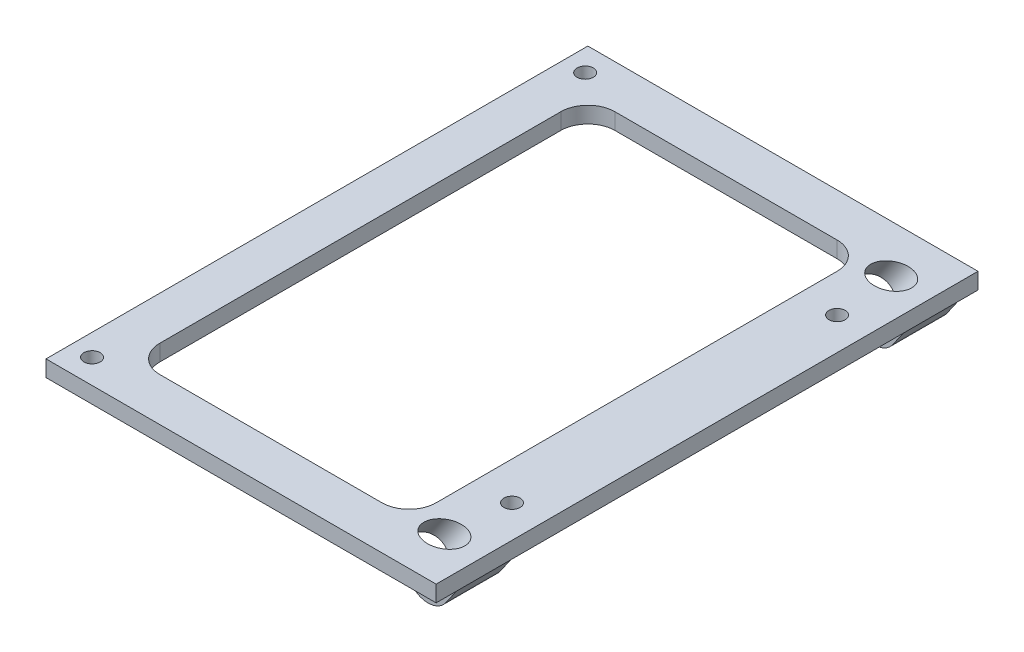
SolidWorks part; units mm, degrees
material "PET"
ref_plane "Front Plane" through (0, 0, 0) normal (0, 0, 1) x (1, 0, 0)
ref_plane "Top Plane" through (0, 0, 0) normal (0, 1, 0) x (1, 0, 0)
ref_plane "Right Plane" through (0, 0, 0) normal (1, 0, 0) x (0, 0, -1)
sketch "Sketch1" plane through (0, 0, 0) normal (0, -1, 0) x (1, 0, 0)
  line L15 (508.5, -88) -> (508.5, 88)
  line L16 (508.5, 88) -> (0.8696, 88)
  line L17 (0.8696, 88) -> (0.8696, -88)
  line L18 (0.8696, -88) -> (508.5, -88)
  line L19 (508.5, -88) -> (508.5, 88)
  line L20 (508.5, 88) -> (0.8696, 88)
  line L21 (0.8696, 88) -> (0.8696, -88)
  line L22 (0.8696, -88) -> (508.5, -88)
  line L54 (11, 0) -> (62, 0) construction
  line L55 (36.5, -42) -> (36.5, 42) construction
  line L57 (70, -50) -> (3, -50)
  line L58 (62, -37) -> (62, 37)
  line L59 (16, -42) -> (57, -42)
  line L60 (57, 42) -> (16, 42)
  line L61 (11, 37) -> (11, -37)
  line L62 (62, -37) -> (62, 37)
  line L63 (16, -42) -> (57, -42)
  line L64 (57, 42) -> (16, 42)
  line L65 (11, 37) -> (11, -37)
  line L66 (70, -50) -> (70, 50)
  line L67 (70, 50) -> (3, 50)
  line L68 (3, -50) -> (3, 50)
  line L69 (70, -50) -> (3, 50) construction
  line L70 (70, 50) -> (3, -50) construction
  line L2167 (70, 50) -> (75, 50)
  line L2168 (70, 50) -> (70, -50)
  line L2169 (70, -50) -> (75, -50)
  line L2170 (75, 50) -> (75, -50)
  circle A3 centre (7, -45.5) radius 1.5
  circle A4 centre (7, -45.5) radius 1.5
  circle A6 centre (7, 45.5) radius 1.5
  circle A7 centre (7, 45.5) radius 1.5
  circle A9 centre (66, -45.5) radius 1.5
  circle A10 centre (66, -45.5) radius 1.5
  circle A12 centre (66, 45.5) radius 1.5
  circle A13 centre (66, 45.5) radius 1.5
  arc A46 (62, 37) -> (57, 42) centre (57, 37) ccw
  arc A47 (57, -42) -> (62, -37) centre (57, -37) ccw
  arc A48 (16, 42) -> (11, 37) centre (16, 37) ccw
  arc A49 (11, -37) -> (16, -42) centre (16, -37) ccw
  arc A50 (62, 37) -> (57, 42) centre (57, 37) ccw
  arc A51 (57, -42) -> (62, -37) centre (57, -37) ccw
  arc A52 (16, 42) -> (11, 37) centre (16, 37) ccw
  arc A53 (11, -37) -> (16, -42) centre (16, -37) ccw
  point P24 (36.5, 0)
  arc M23 (11, 37) -> (16, 42) centre (16, 37) cw
  line M24 (16, 42) -> (57, 42)
  arc M25 (57, 42) -> (62, 37) centre (57, 37) cw
  line M26 (62, 37) -> (62, -37)
  arc M27 (62, -37) -> (57, -42) centre (57, -37) cw
  line M28 (57, -42) -> (16, -42)
  arc M29 (16, -42) -> (11, -37) centre (16, -37) cw
  line M30 (11, -37) -> (11, 37)
  circle M31 centre (66, 45.5) radius 1.5
  circle M34 centre (7, -45.5) radius 1.5
  circle M35 centre (66, -45.5) radius 1.5
  circle M44 centre (7, 45.5) radius 1.5
  dimension "D7" = 8
  dimension "D8" = 8
  dimension "D9" = 5
  dimension "D1" = 0
  dimension "D2" = 0
  dimension "D3" = 0
  dimension "D4" = 0
  dimension "D5" = 0
  dimension "D6" = 0
extrude "Boss-Extrude1" add sketch "Sketch1" along normal blind 3 contours L68 L57 L66 L67 M34 M44 M35 M31 M30 M23 M24 M25 M26 M27 M28 M29 | M35 | L2170 L2167 L66 L2169 | M31 | L63 A51 L62 A50 L64 A52 L65 A53
sketch "Sketch2" plane through (0, 0, -50) normal (0, 0, -1) x (-1, 0, 0)
  line L13 (-3, 0) -> (-75, 0)
  line L14 (-75, 0) -> (-75, -3)
  line L15 (-75, -3) -> (-3, -3)
  line L16 (-3, -3) -> (-3, 0)
  line L17 (-3, 0) -> (-75, 0)
  line L19 (-75, -3) -> (-3, -3)
  line L20 (-3, -3) -> (-3, 0)
  line L23 (-75, 0) -> (-75, -3)
  dimension "D1" = 0
sketch "Sketch3" plane through (0, -3, 0) normal (0, -1, 0) x (1, 0, 0)
  line L5 (62, 37) -> (62, -37) construction
  line L6 (62, -36.2273) -> (75, -36.2273)
  line L7 (62, -36.2273) -> (62, -46.2273)
  line L8 (62, -46.2273) -> (75, -46.2273)
  line L9 (75, -36.2273) -> (75, -46.2273)
  line L10 (75, 50) -> (75, -50) construction
  line L11 (-38.529, -41.2273) -> (75, -41.2273) construction
  line L16 (62, -41.2273) -> (75, -41.2273) construction
  dimension "D1" = 10
extrude "Boss-Extrude3" add sketch "Sketch3" along normal blind 11
sketch "Sketch4" plane through (0, 0, -46.2273) normal (0, 0, -1) x (-1, 0, 0)
  line L0 (-62, -3) -> (-70.7231, -9.108)
  line L1 (-75, -3) -> (-3, -3) construction
  line L2 (-73.7288, 13.759) -> (-78.6437, 10.3175) construction
  line L3 (-75, -3) -> (-67.2977, -14)
  line L4 (-62, -14) -> (-75, -14) construction
  line L5 (-62, -14) -> (-62, -3) construction
  line L14 (-62, -3) -> (-75, -3)
  line L15 (-75, -3) -> (-75, -14)
  line L16 (-75, -14) -> (-62, -14)
  line L17 (-62, -14) -> (-62, -3)
  line L18 (-62, -3) -> (-75, -3)
  line L19 (-75, -3) -> (-75, -14)
  line L20 (-75, -14) -> (-62, -14)
  line L21 (-62, -14) -> (-62, -3)
  line M8 (-75, -3) -> (-75, -14)
  line M9 (-75, -14) -> (-62, -14)
  line M10 (-62, -14) -> (-62, -3)
  dimension "D1" = 0
extrude "Cut-Extrude1" cut sketch "Sketch4" against normal blind 15 contours L0 L3 M9 M10 | L3 M8 M9
sketch "Sketch5" plane through (18.9878, 27.1174, 0) normal (-0.5736, -0.8192, 0) x (0.8192, -0.5736, 0)
  circle A0 centre (55.7058, -41.2841) radius 2.8302
sketch "Sketch6" plane through (18.9878, 27.1174, 0) normal (-0.5736, -0.8192, 0) x (0.8192, -0.5736, 0)
  circle A0 centre (55.5033, -41.2273) radius 3.1
  dimension "D1" = 6.2
extrude "Cut-Extrude2" cut sketch "Sketch6" against normal through all
mirror "Mirror1" about plane through (0, 0, 0) normal (0, 0, 1) of "Cut-Extrude2", "Cut-Extrude1", "Boss-Extrude3"
fillet "Fillet1" radius 4 2 edges at (70.7231, -9.108, -41.2273) (70.7231, -9.108, 41.2273)
sketch "Sketch7" plane through (0, 0, 0) normal (0, 1, 0) x (1, 0, 0)
  line L0 (69, 30) -> (69, -30) construction
  line L1 (69, 0) -> (0, 0) construction
  line L2 (75, -50) -> (75, 50) construction
  circle A0 centre (69, 30) radius 1.5
  circle A1 centre (69, -30) radius 1.5
  dimension "D2" = 3
  dimension "D3" = 3
  dimension "D1" = 6
  dimension "D4" = 60
extrude "Cut-Extrude3" cut sketch "Sketch7" against normal through all
